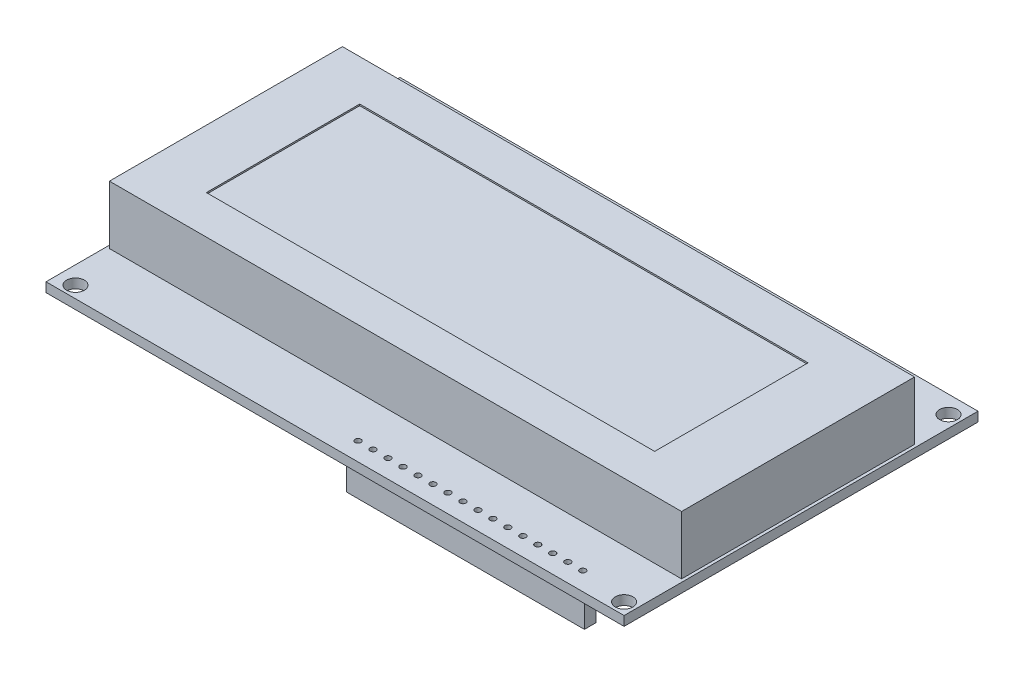
SolidWorks part; units mm, degrees
ref_plane "Front Plane" through (0, 0, 0) normal (0, 0, 1) x (1, 0, 0)
ref_plane "Top Plane" through (0, 0, 0) normal (0, 1, 0) x (1, 0, 0)
ref_plane "Right Plane" through (0, 0, 0) normal (1, 0, 0) x (0, 0, -1)
sketch "Sketch1" plane through (0, 0, 0) normal (0, 1, 0) x (1, 0, 0)
  line L1 (-72.1629, 23.3243) -> (25.8371, 23.3243)
  line L2 (-72.1629, 23.3243) -> (-72.1629, -36.6757)
  line L3 (-72.1629, -36.6757) -> (25.8371, -36.6757)
  line L4 (25.8371, 23.3243) -> (25.8371, -36.6757)
  dimension "D1" = 60
  dimension "D2" = 98
extrude "Boss-Extrude1" add sketch "Sketch1" along normal blind 1.6
sketch "Sketch2" plane through (0, 1.6, 0) normal (0, 1, 0) x (1, 0, 0)
  line L0 (-72.1629, 23.3243) -> (-72.1629, -36.6757) construction
  line L1 (-71.6629, 13.0743) -> (25.3371, 13.0743)
  line L2 (-71.6629, 13.0743) -> (-71.6629, -26.4257)
  line L3 (-71.6629, -26.4257) -> (25.3371, -26.4257)
  line L4 (25.3371, 13.0743) -> (25.3371, -26.4257)
  line L5 (-72.1629, -36.6757) -> (25.8371, -36.6757) construction
  point P4 (-23.1629, 13.0743)
  point P7 (-71.6629, -6.6757)
  dimension "D1" = 97
  dimension "D2" = 39.5
  dimension "D3" = 49
  dimension "D4" = 30
extrude "Boss-Extrude2" add sketch "Sketch2" along normal blind 9.9
sketch "Sketch3" plane through (0, 11.5, 0) normal (0, 1, 0) x (1, 0, 0)
  line L1 (-61.7665, 6.1117) -> (14.2335, 6.1117)
  line L2 (-61.7665, 6.1117) -> (-61.7665, -19.8883)
  line L3 (-61.7665, -19.8883) -> (14.2335, -19.8883)
  line L4 (14.2335, 6.1117) -> (14.2335, -19.8883)
  dimension "D1" = 26
  dimension "D2" = 76
sketch "Sketch4" plane through (0, 1.6, 0) normal (0, 1, 0) x (1, 0, 0)
  line L0 (-72.1629, -36.6757) -> (25.8371, -36.6757) construction
  line L1 (25.8371, -36.6757) -> (25.8371, 23.3243) construction
  circle A0 centre (-69.1629, -34.6757) radius 1.5
  circle A1 centre (23.8371, -34.6757) radius 1.5
  circle A2 centre (-69.1629, 20.3243) radius 1.5
  circle A3 centre (23.8371, 20.3243) radius 1.5
  dimension "D1" = 2
  dimension "D5" = 55
  dimension "D3" = 2
  dimension "D4" = 2
  dimension "D6" = 93
  dimension "D2" = 2
extrude "Cut-Extrude1" cut sketch "Sketch4" against normal blind 1.6
sketch "Sketch5" plane through (0, 1.6, 0) normal (0, 1, 0) x (1, 0, 0)
  line L0 (-72.1629, -36.6757) -> (25.8371, -36.6757) construction
  line L1 (25.8371, -36.6757) -> (25.8371, 23.3243) construction
  circle A0 centre (15.7371, -33.5757) radius 0.5
  circle A1 centre (13.1971, -33.5757) radius 0.5
  circle A2 centre (10.6571, -33.5757) radius 0.5
  circle A3 centre (8.1171, -33.5757) radius 0.5
  circle A4 centre (5.5771, -33.5757) radius 0.5
  circle A5 centre (3.0371, -33.5757) radius 0.5
  circle A6 centre (0.4971, -33.5757) radius 0.5
  circle A7 centre (-2.0429, -33.5757) radius 0.5
  circle A8 centre (-4.5829, -33.5757) radius 0.5
  circle A9 centre (-7.1229, -33.5757) radius 0.5
  circle A10 centre (-9.6629, -33.5757) radius 0.5
  circle A11 centre (-12.2029, -33.5757) radius 0.5
  circle A12 centre (-14.7429, -33.5757) radius 0.5
  circle A13 centre (-17.2829, -33.5757) radius 0.5
  circle A14 centre (-19.8229, -33.5757) radius 0.5
  circle A15 centre (-22.3629, -33.5757) radius 0.5
  dimension "D1" = 16
  dimension "D2" = 3.1
  dimension "D3" = 10.1
extrude "Cut-Extrude2" cut sketch "Sketch5" against normal blind 1.6
sketch "Sketch6" plane through (0, 0, 0) normal (0, -1, 0) x (1, 0, 0)
  line L1 (-23.3982, 34.4744) -> (16.915, 34.4744)
  line L2 (-23.3982, 34.4744) -> (-23.3982, 32.4836)
  line L3 (-23.3982, 32.4836) -> (16.915, 32.4836)
  line L4 (16.915, 34.4744) -> (16.915, 32.4836)
extrude "Boss-Extrude3" add sketch "Sketch6" along normal blind 6
extrude "Cut-Extrude3" cut sketch "Sketch3" against normal blind 0.254
equation "\"D3@Sketch2\" = \"D2@Sketch1\"/2"
equation "\"D4@Sketch2\" = \"D1@Sketch1\"/2"
